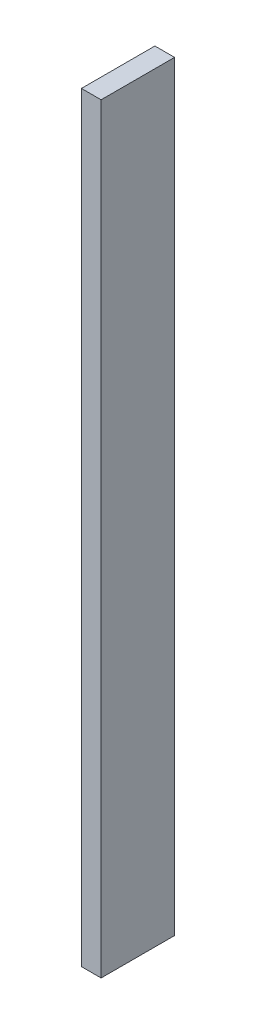
SolidWorks part; units mm, degrees
ref_plane "Front Plane" through (0, 0, 0) normal (0, 0, 1) x (1, 0, 0)
ref_plane "Top Plane" through (0, 0, 0) normal (0, 1, 0) x (1, 0, 0)
ref_plane "Right Plane" through (0, 0, 0) normal (1, 0, 0) x (0, 0, -1)
sketch "Sketch1" plane through (0, 0, 0) normal (1, 0, 0) x (0, 0, -1)
  line L1 (0, 0) -> (11.2, 0)
  line L2 (0, 0) -> (0, 115.957)
  line L3 (0, 115.957) -> (11.2, 115.957)
  line L4 (11.2, 0) -> (11.2, 115.957)
sketch "Sketch2" plane through (0, 0, 0) normal (0, 1, 0) x (1, 0, 0)
  line L1 (-3, 0) -> (0, 0)
  line L2 (-3, 0) -> (-3, 11.2)
  line L3 (-3, 11.2) -> (0, 11.2)
  line L4 (0, 0) -> (0, 11.2)
extrude "Boss-Extrude1" add sketch "Sketch1" against normal up to vertex (3 mm away) up to point (-3, 0, 0)
